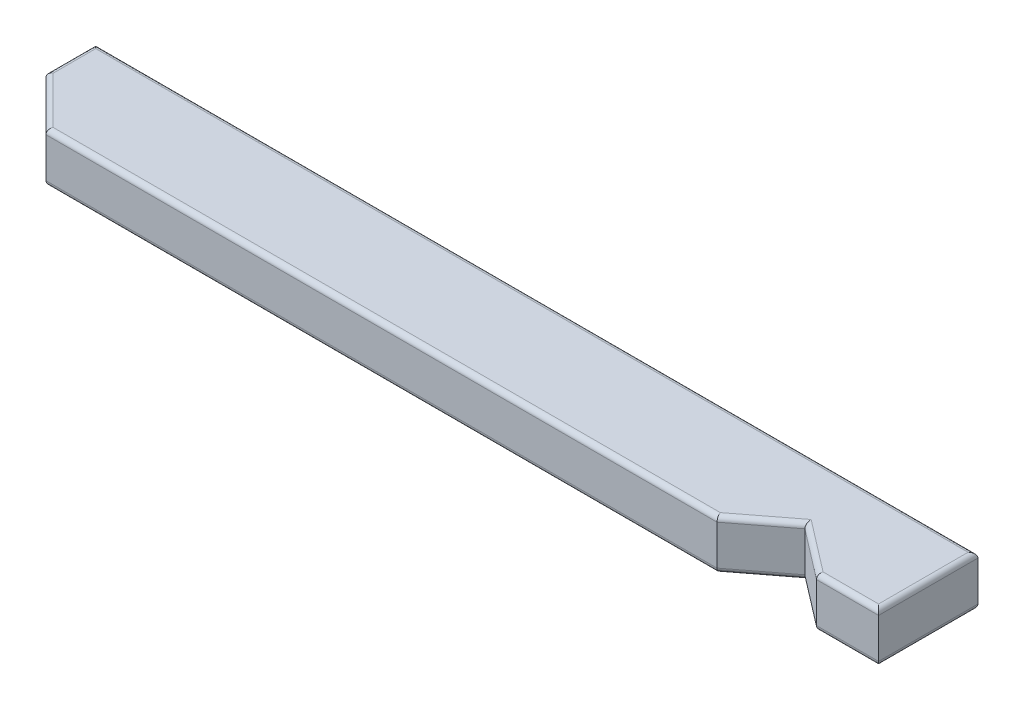
SolidWorks part; units mm, degrees
material "Balsa"
ref_plane "Front Plane" through (0, 0, 0) normal (0, 0, 1) x (1, 0, 0)
ref_plane "Top Plane" through (0, 0, 0) normal (0, 1, 0) x (1, 0, 0)
ref_plane "Right Plane" through (0, 0, 0) normal (1, 0, 0) x (0, 0, -1)
sketch "Sketch1" plane through (0, -12.7, 0) normal (0, -1, 0) x (-1, 0, 0)
  line L0 (-2714.3, -292.78) -> (-2714.3, -384.22) construction
  line L1 (-2714.3, 389.3) -> (-1812.7, 389.3)
  line L2 (-2714.3, 389.3) -> (-2714.3, 287.7)
  line L3 (-2714.3, 287.7) -> (-1812.7, 287.7)
  line L4 (-1812.7, 389.3) -> (-1812.7, 287.7)
  line L5 (-1812.7, -384.22) -> (-1812.7, -292.78) construction
  line L6 (-1803.322, 287.7) -> (-2600, 287.7) construction
  dimension "D1" = 101.6
extrude "Boss-Extrude1" add sketch "Sketch1" against normal blind 50.8
sketch "Sketch3" plane through (0, 38.1, 0) normal (0, 1, 0) x (1, 0, 0)
  line L0 (2549.2, 287.7) -> (2600, 326.6802)
  line L1 (2714.3, 287.7) -> (1812.7, 287.7) construction
  line L2 (2600, 326.6802) -> (2650.8, 287.7)
  line L3 (2600, 326.6802) -> (2600, 287.7) construction
  line L4 (2714.3, 389.3) -> (2714.3, 287.7) construction
  line L5 (2549.2, 287.7) -> (2650.8, 287.7)
  line L6 (1812.7, 338.5) -> (1812.7, 287.7)
  line L7 (1812.7, 287.7) -> (1812.7, 389.3) construction
  line L8 (1812.7, 287.7) -> (1863.5, 287.7)
  line L9 (1863.5, 287.7) -> (1812.7, 338.5)
  dimension "D1" = 105
  dimension "D2" = 114.3
  dimension "D3" = 101.6
  dimension "D4" = 45
  dimension "D5" = 50.8
extrude "Cut-Extrude1" cut sketch "Sketch3" against normal through all
fillet "Fillet1" radius 5.08 16 edges at (2682.55, -12.7, -287.7) (2263.5, -12.7, -389.3) (2682.55, 38.1, -287.7) (2263.5, 38.1, -389.3) (2206.35, -12.7, -287.7) (1812.7, -12.7, -363.9) (1812.7, 38.1, -363.9) (2206.35, 38.1, -287.7) (2714.3, -12.7, -338.5) (2714.3, 38.1, -338.5) (2625.4, -12.7, -307.1901) (2574.6, -12.7, -307.1901) (2625.4, 38.1, -307.1901) (2574.6, 38.1, -307.1901) (1838.1, -12.7, -313.1) (1838.1, 38.1, -313.1)
